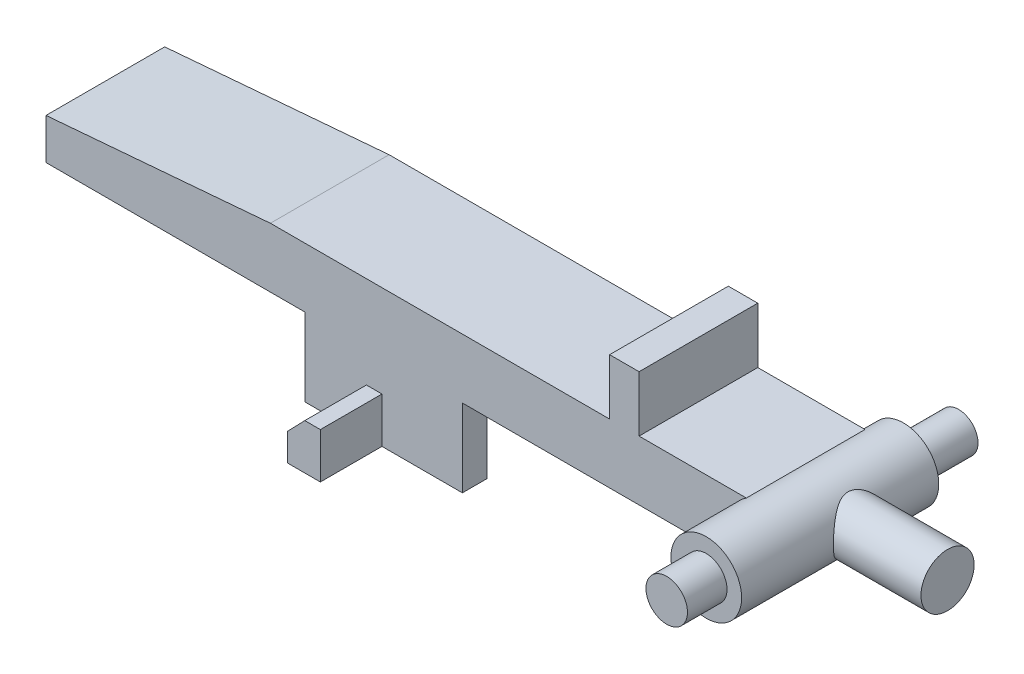
SolidWorks part; units mm, degrees
ref_plane "Front Plane" through (0, 0, 0) normal (0, 0, 1) x (1, 0, 0)
ref_plane "Top Plane" through (0, 0, 0) normal (0, 1, 0) x (1, 0, 0)
ref_plane "Right Plane" through (0, 0, 0) normal (1, 0, 0) x (0, 0, -1)
sketch "Sketch1" plane through (0, 0, 0) normal (0, 0, 1) x (1, 0, 0)
  line L0 (0, 0) -> (54.25, 0)
  line L1 (54.25, 0) -> (54.25, 4.6)
  line L4 (54.25, 4.6) -> (44.52, 4.6)
  line L5 (44.52, 4.6) -> (44.52, 8.9)
  line L6 (44.52, 8.9) -> (42.25, 8.9)
  line L7 (42.25, 8.9) -> (42.25, 4.6)
  line L8 (42.25, 4.6) -> (16.1, 4.6)
  line L9 (0, 0) -> (0, 3.25)
  line L10 (0, 3.25) -> (16.1, 4.6)
  line L11 (16.1, 4.6) -> (-3.604, 4.6) construction
  dimension "D1" = 54.25
  dimension "D2" = 3.25
  dimension "D3" = 4.793
  dimension "D4" = 4.3
  dimension "D5" = 2.27
  dimension "D6" = 12
  dimension "D7" = 16.1
  dimension "D8" = 1.35
extrude "Boss-Extrude1" add sketch "Sketch1" against normal blind 9.15
sketch "Sketch4" plane through (0, 0, 0) normal (0, -1, 0) x (1, 0, 0)
  line L8 (54.25, -9.15) -> (54.25, 0) construction
  line L9 (54.25, -7.25) -> (54.25, -1.9)
  line L11 (54.25, -7.25) -> (1.9, -7.25)
  line L12 (1.9, -7.25) -> (1.9, -1.9)
  line L13 (1.9, -1.9) -> (54.25, -1.9)
  line L14 (54.25, -7.25) -> (1.9, -7.25)
  line L15 (1.9, -7.25) -> (1.9, -1.9)
  line L16 (1.9, -1.9) -> (54.25, -1.9)
  dimension "D1" = 1.9
extrude "Cut-Extrude2" cut sketch "Sketch4" against normal blind 3
ref_plane "Plane1" through (0, 0, -10.65) normal (0, 0, -1) x (-1, 0, 0)
sketch "Sketch6" plane through (0, 0, -10.65) normal (0, 0, -1) x (-1, 0, 0)
  line L0 (-54.25, 0) -> (-54.25, 4.6) construction
  circle A0 centre (-54.25, 2.3) radius 2.725
  dimension "D1" = 5.45
extrude "Boss-Extrude2" add sketch "Sketch6" against normal blind 13.65
ref_plane "Plane2" through (0, 0, -17.9) normal (0, 0, 1) x (1, 0, 0)
sketch "Sketch8" plane through (0, 0, -17.9) normal (0, 0, 1) x (1, 0, 0)
  circle A0 centre (54.25, 2.3) radius 1.5
  dimension "D1" = 3
extrude "Boss-Extrude3" add sketch "Sketch8" along normal up to surface (8.75 mm away) up to face at (32.6615, 4.3833, -9.15)
sketch "Sketch9" plane through (0, 0, 3) normal (0, 0, 1) x (1, 0, 0)
  circle A0 centre (54.25, 2.3) radius 1.6
  dimension "D1" = 3.2
extrude "Boss-Extrude4" add sketch "Sketch9" along normal blind 4.6
sketch "Sketch10" plane through (0, 3, 0) normal (0, -1, 0) x (1, 0, 0)
  line L1 (0, -9.15) -> (0, 0) construction
  line L3 (-4.895, -10.65) -> (4.895, -10.65) construction
  circle A0 centre (20.95, -5.325) radius 0.925
  circle A1 centre (20.95, -5.325) radius 2.6
  dimension "D1" = 1.85
  dimension "D2" = 5.2
  dimension "D3" = 20.95
  dimension "D4" = 5.325
extrude "Boss-Extrude5" add sketch "Sketch10" along normal blind 7.55
sketch "Sketch11" plane through (0, 0, 0) normal (0, 0, 1) x (1, 0, 0)
  line L0 (30.9, 0) -> (30.9, -6)
  line L1 (0, 0) -> (52.7886, 0) construction
  line L2 (30.9, -6) -> (18.75, -6)
  line L3 (18.75, -6) -> (18.75, 0)
  line L4 (18.75, 0) -> (30.9, 0)
  line L5 (0, 3.25) -> (0, 0) construction
  dimension "D1" = 12.15
  dimension "D2" = 6
  dimension "D3" = 18.75
extrude "Boss-Extrude6" add sketch "Sketch11" against normal up to surface (1.9 mm away) up to face at (26.9286, 1.4521, -1.9)
sketch "Sketch12" plane through (0, 0, 0) normal (0, 0, 1) x (1, 0, 0)
  line L0 (24.7, -6) -> (24.7, -2.5)
  line L2 (18.75, -6) -> (30.9, -6) construction
  line L3 (24.7, -2.5) -> (23.5, -2.5)
  line L5 (22.15, -3.9) -> (22.15, -6)
  line L6 (22.15, -6) -> (24.7, -6)
  line L9 (22.15, -3.9) -> (23.5, -2.5)
  line L10 (18.75, 0) -> (18.75, -6) construction
  dimension "D1" = 2.55
  dimension "D2" = 1.2
  dimension "D3" = 133.958
  dimension "D4" = 3.5
  dimension "D5" = 5.95
extrude "Boss-Extrude7" add sketch "Sketch12" along normal blind 4.75
ref_plane "Plane3" through (54.3, 0, 0) normal (1, 0, 0) x (0, 0, -1)
sketch "Sketch13" plane through (54.3, 0, 0) normal (1, 0, 0) x (0, 0, -1)
  line L1 (9.15, 8.9) -> (0, 8.9) construction
  line L2 (10.65, -0.425) -> (10.65, 5.025) construction
  circle A0 centre (4.575, 2.3) radius 2.05
  point P8 (4.575, 8.9)
  point P12 (10.65, 2.3)
  dimension "D1" = 4.1
extrude "Boss-Extrude8" add sketch "Sketch13" along normal blind 9.425
fillet "Fillet1" radius 0.5 2 edges at (0, 1.625, -9.15) (0, 1.625, 0)
sketch "Sketch16" plane through (63.725, 0, 0) normal (1, 0, 0) x (0, 0, -1)
  point P0 (4.575, 2.3)
ref_plane "Plane5" through (0, 0, -4.575) normal (0, 0, 1) x (1, 0, 0)
sketch "Sketch17" plane through (0, 0, -4.575) normal (0, 0, 1) x (1, 0, 0)
  line L0 (63.725, 2.3) -> (79.0342, 2.3)
sketch "Sketch18" plane through (54.3, 0, 0) normal (1, 0, 0) x (0, 0, -1)
  line L0 (-7.6, 3.9) -> (-7.6, 0.7) construction
  line L1 (-7.6, 3.9) -> (-7.6, 0.7)
  line L2 (-10.2447, 2.3) -> (20.8398, 2.3)
  line L3 (-10.2447, 2.3) -> (20.8398, 2.3) construction
  line L4 (17.9, 0.8) -> (17.9, 3.8) construction
  line L5 (17.9, 0.8) -> (17.9, 3.8)
  point P4 (-7.6, 2.3)
  point P9 (17.9, 2.3)
  dimension "D1" = 31.0845
  dimension "D2" = 2.6447
sketch "Sketch19" plane through (0, 0, 0) normal (0, 0, 1) x (1, 0, 0)
  line L0 (0.5, 0) -> (-1.2, 0)
  line L1 (-1.2, 0) -> (-1.2, 3.1494)
  line L2 (-1.2, 3.1494) -> (0.5, 3.2919)
  line L3 (16.1, 4.6) -> (0.5, 3.2919) construction
  line L4 (0.5, 0) -> (0.5, 3.2919)
  line L21 (16.1, 4.6) -> (0.5, 3.2919)
  line L22 (0.5, 3.2919) -> (0.5, 0)
  line L23 (0.5, 0) -> (18.75, 0)
  line L24 (18.75, 0) -> (18.75, -6)
  line L25 (18.75, -6) -> (22.15, -6)
  line L26 (22.15, -6) -> (22.15, -3.9)
  line L27 (22.15, -3.9) -> (23.5, -2.5)
  line L28 (23.5, -2.5) -> (24.7, -2.5)
  line L29 (24.7, -2.5) -> (24.7, -6)
  line L30 (24.7, -6) -> (30.9, -6)
  line L31 (30.9, -6) -> (30.9, 0)
  line L32 (30.9, 0) -> (52.7886, 0)
  line L33 (52.7886, 4.6) -> (44.52, 4.6)
  line L34 (44.52, 4.6) -> (44.52, 8.9)
  line L35 (44.52, 8.9) -> (42.25, 8.9)
  line L36 (42.25, 8.9) -> (42.25, 4.6)
  line L37 (42.25, 4.6) -> (16.1, 4.6)
  line L40 (0.5, 0) -> (18.75, 0)
  line L41 (18.75, 0) -> (18.75, -6)
  line L42 (18.75, -6) -> (22.15, -6)
  line L43 (22.15, -6) -> (22.15, -3.9)
  line L44 (22.15, -3.9) -> (23.5, -2.5)
  line L45 (23.5, -2.5) -> (24.7, -2.5)
  line L46 (24.7, -2.5) -> (24.7, -6)
  line L47 (24.7, -6) -> (30.9, -6)
  line L48 (30.9, -6) -> (30.9, 0)
  line L49 (30.9, 0) -> (52.7886, 0)
  line L50 (52.7886, 4.6) -> (44.52, 4.6)
  line L51 (44.52, 4.6) -> (44.52, 8.9)
  line L52 (44.52, 8.9) -> (42.25, 8.9)
  line L53 (42.25, 8.9) -> (42.25, 4.6)
  line L54 (42.25, 4.6) -> (16.1, 4.6)
  arc A1 (52.7886, 4.6) -> (52.7886, 0) centre (54.25, 2.3) ccw
  arc A2 (52.7886, 4.6) -> (52.7886, 0) centre (54.25, 2.3) ccw
  dimension "D1" = 1.7
  dimension "D2" = 0
extrude "Boss-Extrude9" add sketch "Sketch19" against normal up to surface (9.15 mm away) contours L0 L1 L2 L4 up to face at (32.7726, 4.388, -9.15)
sketch "Sketch20" plane through (0, 0, 3) normal (0, 0, 1) x (1, 0, 0)
  circle A1 centre (54.25, 2.3) radius 2.725
  circle A2 centre (54.25, 2.3) radius 2.725
  dimension "D1" = 0
extrude "Boss-Extrude10" add sketch "Sketch20" along normal blind 1.55
sketch "Sketch21" plane through (0, 0, -17.9) normal (0, 0, -1) x (-1, 0, 0)
  circle A1 centre (-54.25, 2.3) radius 1.5
  circle A2 centre (-54.25, 2.3) radius 1.5
  dimension "D1" = 0
extrude "Cut-Extrude3" cut sketch "Sketch21" against normal blind 3
